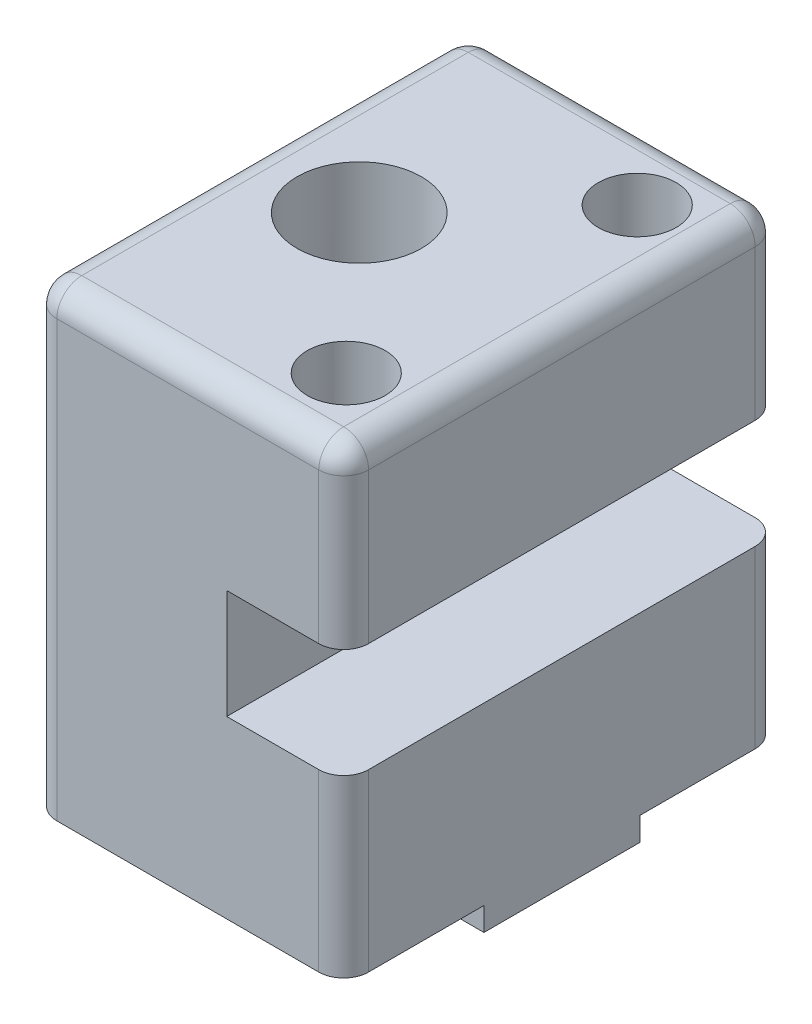
SolidWorks part; units mm, degrees
ref_plane "Front Plane" through (0, 0, 0) normal (0, 0, 1) x (1, 0, 0)
ref_plane "Top Plane" through (0, 0, 0) normal (0, 1, 0) x (1, 0, 0)
ref_plane "Right Plane" through (0, 0, 0) normal (1, 0, 0) x (0, 0, -1)
sketch "Sketch1" plane through (0, 0, 0) normal (0, 0, 1) x (1, 0, 0)
  line L0 (0, 0) -> (15.875, 0) construction
  line L1 (15.875, 23.4156) -> (-15.875, 23.4156)
  line L2 (15.875, 23.4156) -> (15.875, 5.5562)
  line L3 (15.875, -23.4156) -> (-15.875, -23.4156)
  line L4 (-15.875, 23.4156) -> (-15.875, -23.4156)
  line L5 (15.875, 23.4156) -> (-15.875, -23.4156) construction
  line L6 (15.875, -23.4156) -> (-15.875, 23.4156) construction
  line L7 (15.875, 5.5562) -> (3.9687, 5.5562)
  line L8 (3.9687, 5.5562) -> (3.9687, -5.5563)
  line L9 (15.875, -5.5562) -> (3.9687, -5.5563)
  line L10 (15.875, -5.5562) -> (15.875, -23.4156)
  point P0 (0, 0)
  point P12 (3.9687, 0)
  dimension "D1" = 46.8312
  dimension "D2" = 31.75
  dimension "D3" = 5.5562
  dimension "D4" = 11.9062
extrude "Boss-Extrude1" add sketch "Sketch1" along normal mid plane 44.45
sketch "Sketch4" plane through (15.875, 0, 0) normal (1, 0, 0) x (0, 0, -1)
  line L0 (0, -23.4156) -> (0, -5.5563) construction
  line L1 (-22.225, -23.4156) -> (22.225, -23.4156) construction
  line L2 (-22.225, -5.5563) -> (22.225, -5.5563) construction
  line L3 (-7.9375, -23.4156) -> (-7.9375, -25.7969)
  line L4 (-7.9375, -25.7969) -> (7.9375, -25.7969)
  line L5 (7.9375, -23.4156) -> (7.9375, -25.7969)
  line L6 (-7.9375, -23.4156) -> (7.9375, -23.4156)
  point P12 (0, -25.7969)
  dimension "D1" = 7.9375
  dimension "D2" = 2.3813
extrude "Boss-Extrude2" add sketch "Sketch4" against normal through all
sketch "Sketch2" plane through (0, 23.4156, 0) normal (0, 1, 0) x (1, 0, 0)
  line L0 (15.875, -22.225) -> (15.875, 22.225) construction
  line L1 (1.5875, -6.35) -> (-11.1125, -6.35) construction
  line L2 (1.5875, -6.35) -> (1.5875, 6.35) construction
  line L3 (1.5875, 6.35) -> (-11.1125, 6.35) construction
  line L4 (-11.1125, -6.35) -> (-11.1125, 6.35) construction
  line L5 (1.5875, -6.35) -> (-11.1125, 6.35) construction
  line L6 (1.5875, 6.35) -> (-11.1125, -6.35) construction
  circle A0 centre (-4.7625, 0) radius 8.9803 construction
  circle A1 centre (-4.7625, 0) radius 6.331
  dimension "D3" = 12.6619
  dimension "D1" = 12.7
  dimension "D2" = 20.6375
extrude "Cut-Extrude1" cut sketch "Sketch2" against normal through all and the other way through all
sketch "Sketch3" plane through (0, 23.4156, 0) normal (0, 1, 0) x (1, 0, 0)
  line L0 (0, 0) -> (15.875, 0) construction
  line L1 (15.875, -22.225) -> (15.875, 22.225) construction
  circle A0 centre (8.7312, 14.8167) radius 3.9688
  circle A1 centre (8.7312, -14.8167) radius 3.9688
  dimension "D1" = 7.9375
  dimension "D2" = 7.1437
  dimension "D3" = 14.8167
extrude "Cut-Extrude2" cut sketch "Sketch3" against normal up to next
fillet "Fillet1" radius 2.54 10 edges at (-15.875, 0, -22.225) (15.875, 14.4859, -22.225) (15.875, -14.4859, -22.225) (15.875, -14.4859, 22.225) (15.875, 14.4859, 22.225) (-15.875, 0, 22.225) (-15.875, 23.4156, 0) (15.875, 23.4156, 0) (0, 23.4156, 22.225) (0, 23.4156, -22.225)
